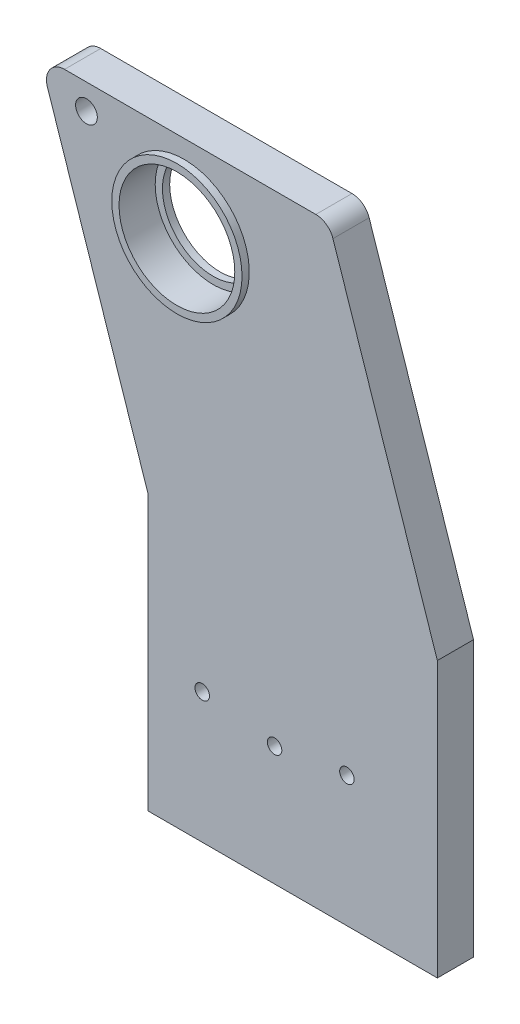
SolidWorks part; units mm, degrees
material "Alloy Steel (SS)"
ref_plane "Front Plane" through (0, 0, 0) normal (0, 0, 1) x (1, 0, 0)
ref_plane "Top Plane" through (0, 0, 0) normal (0, 1, 0) x (1, 0, 0)
ref_plane "Right Plane" through (0, 0, 0) normal (1, 0, 0) x (0, 0, -1)
sketch "Sketch1" plane through (0, 0, 0) normal (0, 0, 1) x (1, 0, 0)
  line L0 (-40, 83) -> (-70, 83)
  line L1 (10, 83) -> (-40, 83)
  line L2 (40, -7) -> (40, -83)
  line L3 (40, -83) -> (-40, -83)
  line L4 (-40, -7) -> (-40, -83)
  line L5 (40, 83) -> (-40, -83) construction
  line L6 (40, -83) -> (-40, 83) construction
  line L7 (-70, 83) -> (-40, -7)
  line L8 (40, 83) -> (40, -7) construction
  line L9 (10, 83) -> (40, -7)
  circle A0 centre (-30, 60) radius 16
  point P0 (0, 0)
  point P12 (-40, -80)
  dimension "D10" = 32
  dimension "D1" = 80
  dimension "D2" = 166
  dimension "D3" = 30
  dimension "D4" = 90
  dimension "D5" = 30
  dimension "D6" = 90
  dimension "D7" = 83
  dimension "D8" = 83
  dimension "D9" = 40
  dimension "D11" = 30
  dimension "D12" = 143
  dimension "D13" = 163
extrude "Boss-Extrude1" add sketch "Sketch1" along normal blind 10
sketch "Sketch2" plane through (0, 0, 10) normal (0, 0, 1) x (1, 0, 0)
  circle A0 centre (-30, 60) radius 16
  circle A1 centre (-30, 60) radius 18
  dimension "D1" = 36
  dimension "D2" = 32
extrude "Boss-Extrude2" add sketch "Sketch2" along normal blind 2
sketch "Sketch3" plane through (0, 0, 0) normal (0, 0, -1) x (-1, 0, 0)
  line L0 (40, -7) -> (40, -83) construction
  line L1 (40, -83) -> (-40, -83) construction
  circle A0 centre (-15, -47) radius 2
  circle A1 centre (25, -47) radius 2
  dimension "D3" = 4
  dimension "D4" = 4
  dimension "D1" = 15
  dimension "D2" = 55
  dimension "D5" = 36
extrude "Cut-Extrude1" cut sketch "Sketch3" against normal blind 10
sketch "Sketch4" plane through (0, 0, 0) normal (0, 0, -1) x (-1, 0, 0)
  line L3 (40, -7) -> (40, -83) construction
  line L7 (40, -83) -> (-40, -83) construction
  circle A0 centre (5, -50) radius 2
  dimension "D3" = 4
  dimension "D1" = 35
  dimension "D2" = 33
extrude "Cut-Extrude2" cut sketch "Sketch4" against normal blind 10
sketch "Sketch5" plane through (0, 0, 0) normal (0, 0, -1) x (-1, 0, 0)
  line L0 (-10, 83) -> (70, 83) construction
  circle A0 centre (57, 76) radius 3
  dimension "D1" = 6
  dimension "D2" = 13
  dimension "D3" = 7
extrude "Cut-Extrude3" cut sketch "Sketch5" against normal up to next
fillet "Fillet1" radius 5 2 edges at (10, 83, 5) (-70, 83, 5)
sketch "Sketch6" plane through (0, 0, 0) normal (0, 0, -1) x (-1, 0, 0)
  point P0 (30, 60)
sketch "Sketch8" plane through (0, 0, 0) normal (0, 0, -1) x (-1, 0, 0)
  circle A0 centre (30, 60) radius 16 construction
  circle A1 centre (30, 60) radius 16
  circle A2 centre (30, 60) radius 14
  dimension "D1" = 2
extrude "Boss-Extrude4" add sketch "Sketch8" along normal blind 2 from offset 2
